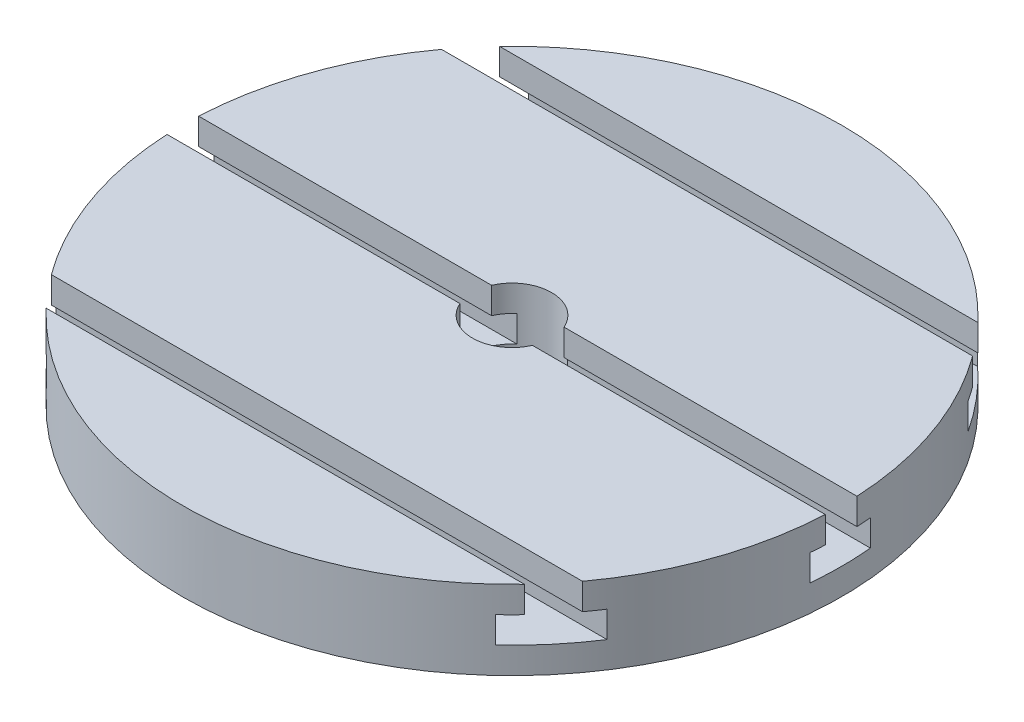
SolidWorks part; units mm, degrees
ref_plane "Спереди" through (0, 0, 0) normal (0, 0, 1) x (1, 0, 0)
ref_plane "Сверху" through (0, 0, 0) normal (0, 1, 0) x (1, 0, 0)
ref_plane "Справа" through (0, 0, 0) normal (1, 0, 0) x (0, 0, -1)
sketch "Эскиз1" plane through (0, 0, 0) normal (1, 0, 0) x (0, 0, -1)
  line L0 (0, -12.6281) -> (0, 29.9138) construction
  line L1 (15, 0) -> (125, 0)
  line L2 (15, 0) -> (15, 30)
  line L3 (15, 30) -> (125, 30)
  line L4 (125, 0) -> (125, 30)
revolve "Повернуть1" add sketch "Эскиз1" angle 360 about L0
sketch "Эскиз2" plane through (0, 0, 0) normal (1, 0, 0) x (0, 0, -1)
  line L1 (11.5, 10) -> (11.5, 20)
  line L2 (11.5, 20) -> (6, 20)
  line L3 (6, 20) -> (6, 30)
  line L4 (125, 30) -> (-125, 30) construction
  line L5 (6, 30) -> (-6, 30)
  line L6 (15, 30) -> (-15, 30) construction
  line L10 (0, 28.7888) -> (0, -3.461) construction
  line L11 (-6, 20) -> (-6, 30)
  line L12 (-11.5, 20) -> (-6, 20)
  line L13 (-11.5, 10) -> (-11.5, 20)
  line L14 (-11.5, 10) -> (11.5, 10)
  line L15 (68.5, 10) -> (91.5, 10)
  line L16 (91.5, 10) -> (91.5, 20)
  line L17 (91.5, 20) -> (86, 20)
  line L18 (86, 20) -> (86, 30)
  line L19 (86, 30) -> (74, 30)
  line L20 (74, 20) -> (74, 30)
  line L21 (68.5, 20) -> (74, 20)
  line L22 (68.5, 10) -> (68.5, 20)
  line L24 (-91.5, 10) -> (-68.5, 10)
  line L25 (-68.5, 10) -> (-68.5, 20)
  line L26 (-68.5, 20) -> (-74, 20)
  line L27 (-74, 20) -> (-74, 30)
  line L28 (-74, 30) -> (-86, 30)
  line L29 (-86, 20) -> (-86, 30)
  line L30 (-91.5, 20) -> (-86, 20)
  line L31 (-91.5, 10) -> (-91.5, 20)
  point P0 (0, 10)
  point P12 (0, 30)
  point P26 (80, 30)
  point P37 (-80, 30)
  dimension "D1" = 6
  dimension "D2" = 11.5
  dimension "D3" = 10
  dimension "D4" = 10
  dimension "D5" = 2
  dimension "D6" = 2
extrude "Вырез-Вытянуть1" cut sketch "Эскиз2" against normal mid plane 300
